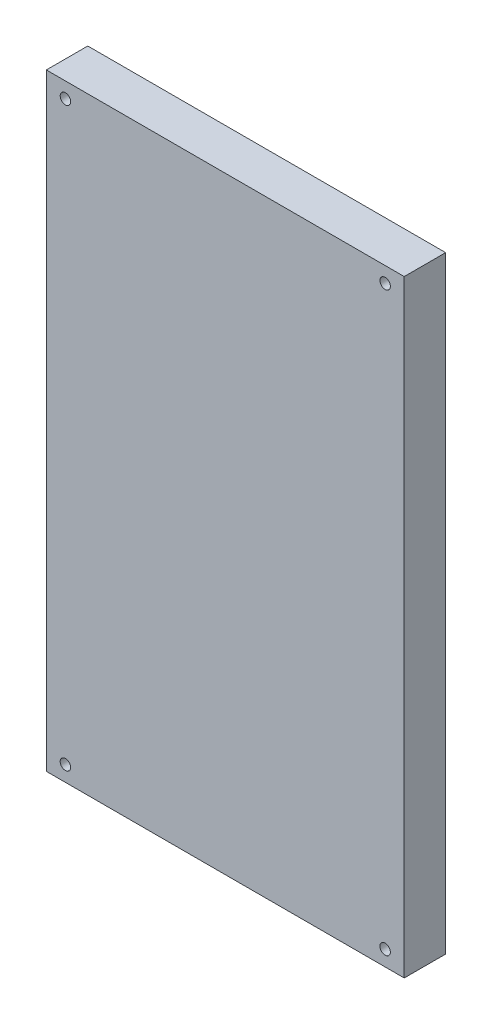
SolidWorks part; units mm, degrees
ref_plane "Front Plane" through (0, 0, 0) normal (0, 0, 1) x (1, 0, 0)
ref_plane "Top Plane" through (0, 0, 0) normal (0, 1, 0) x (1, 0, 0)
ref_plane "Right Plane" through (0, 0, 0) normal (1, 0, 0) x (0, 0, -1)
sketch "Sketch1" plane through (0, 0, 0) normal (0, 0, 1) x (1, 0, 0)
  line L0 (0, 92) -> (108.4, 92) construction
  line L1 (0, 0) -> (108.4, 0)
  line L2 (0, 0) -> (0, 184)
  line L3 (0, 184) -> (108.4, 184)
  line L4 (108.4, 0) -> (108.4, 184)
  line L5 (54.2, 184) -> (54.2, 0) construction
  line L6 (5.7812, 4.6875) -> (102.6187, 4.6875) construction
  line L7 (5.7812, 179.3125) -> (5.7812, 4.6875) construction
  circle A0 centre (5.7812, 4.6875) radius 1.5875
  circle A1 centre (102.6187, 4.6875) radius 1.5875
  circle A2 centre (5.7812, 179.3125) radius 1.5875
  circle A3 centre (102.6187, 179.3125) radius 1.5875
  point P17 (5.7812, 92)
  point P18 (54.2, 4.6875)
  point P19 (104.403, 178.9649)
  point P20 (102.6187, 178.1389)
  point P21 (103.9831, 179.3125)
  point P22 (0, 0)
  dimension "D5" = 3.175
  dimension "D1" = 184
  dimension "D2" = 108.4
  dimension "D3" = 174.625
  dimension "D4" = 96.8375
extrude "Boss-Extrude1" add sketch "Sketch1" along normal blind 12.55
